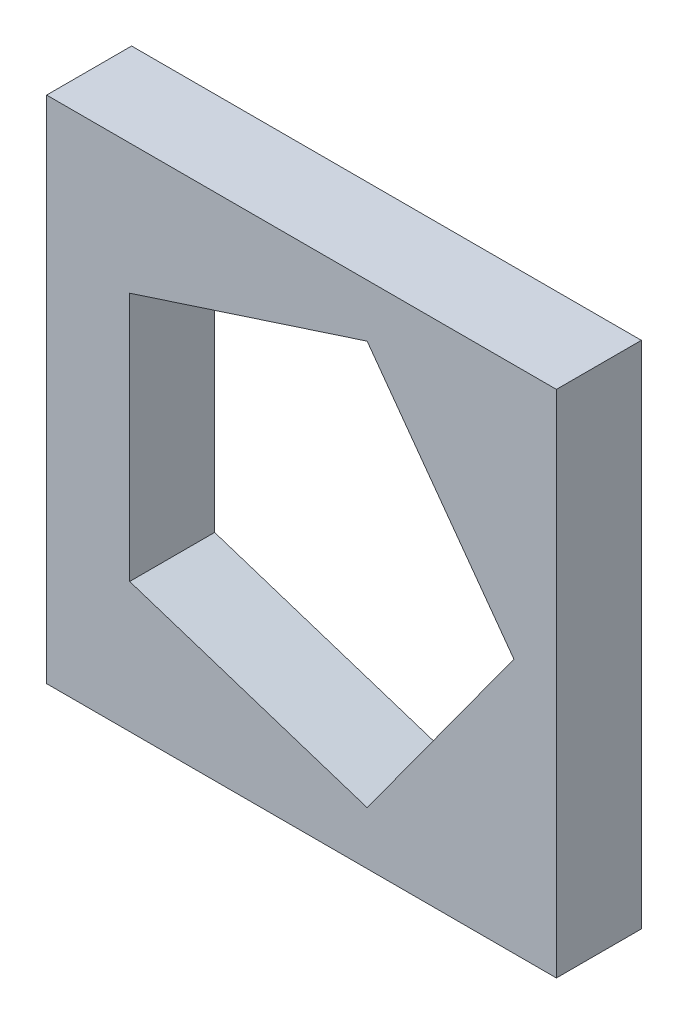
SolidWorks part; units mm, degrees
ref_plane "Piano frontale" through (0, 0, 0) normal (0, 0, 1) x (1, 0, 0)
ref_plane "Piano superiore" through (0, 0, 0) normal (0, 1, 0) x (1, 0, 0)
ref_plane "Piano destro" through (0, 0, 0) normal (1, 0, 0) x (0, 0, -1)
sketch "Schizzo1" plane through (0, 0, 0) normal (0, 0, 1) x (1, 0, 0)
  line L0 (7.7254, -23.7764) -> (25, 0)
  line L1 (-30, 30) -> (30, 30)
  line L2 (-30, 30) -> (-30, -30)
  line L3 (-30, -30) -> (30, -30)
  line L4 (30, 30) -> (30, -30)
  line L5 (25, 0) -> (7.7254, 23.7764)
  line L6 (7.7254, 23.7764) -> (-20.2254, 14.6946)
  line L7 (-20.2254, 14.6946) -> (-20.2254, -14.6946)
  line L8 (-20.2254, -14.6946) -> (7.7254, -23.7764)
  circle A0 centre (0, 0) radius 25 construction
  dimension "D1" = 60
  dimension "D2" = 60
  dimension "D3" = 30
extrude "Estrusione-Estrusione1" add sketch "Schizzo1" along normal blind 10 contours L5 L6 L7 L8 L0 | L1 L4 L3 L2
